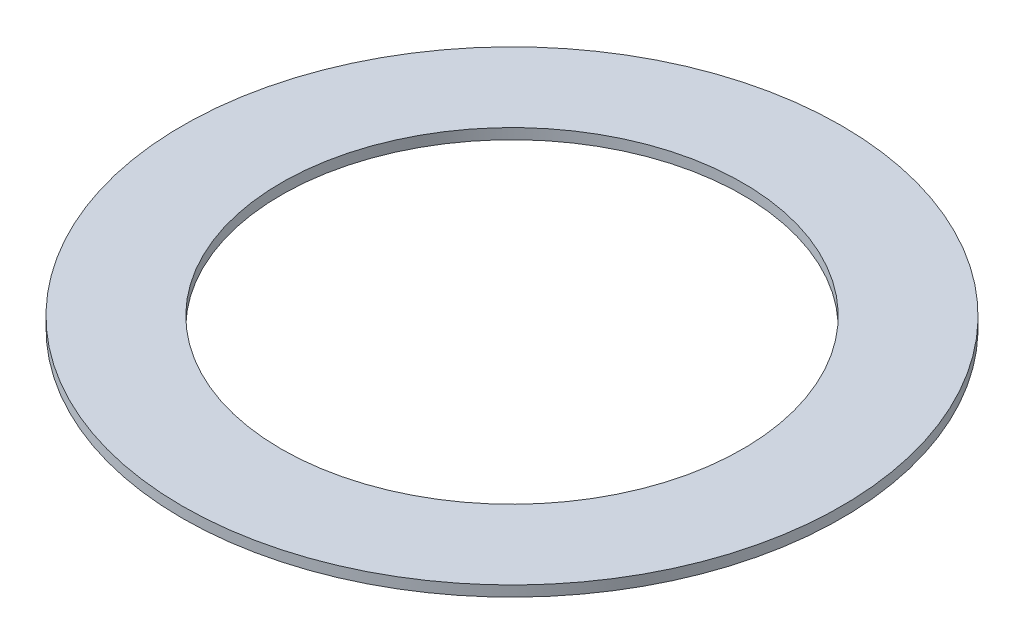
SolidWorks part; units mm, degrees
material "POM Acetal Copolymer"
ref_plane "Front Plane" through (0, 0, 0) normal (0, 0, 1) x (1, 0, 0)
ref_plane "Top Plane" through (0, 0, 0) normal (0, 1, 0) x (1, 0, 0)
ref_plane "Right Plane" through (0, 0, 0) normal (1, 0, 0) x (0, 0, -1)
sketch "Sketch1" plane through (0, 0, 0) normal (0, 1, 0) x (1, 0, 0)
  circle A0 centre (0, 0) radius 11.1125
  circle A1 centre (0, 0) radius 15.875
  dimension "D1" = 31.75
  dimension "D2" = 22.225
extrude "Boss-Extrude1" add sketch "Sketch1" along normal blind 0.508
